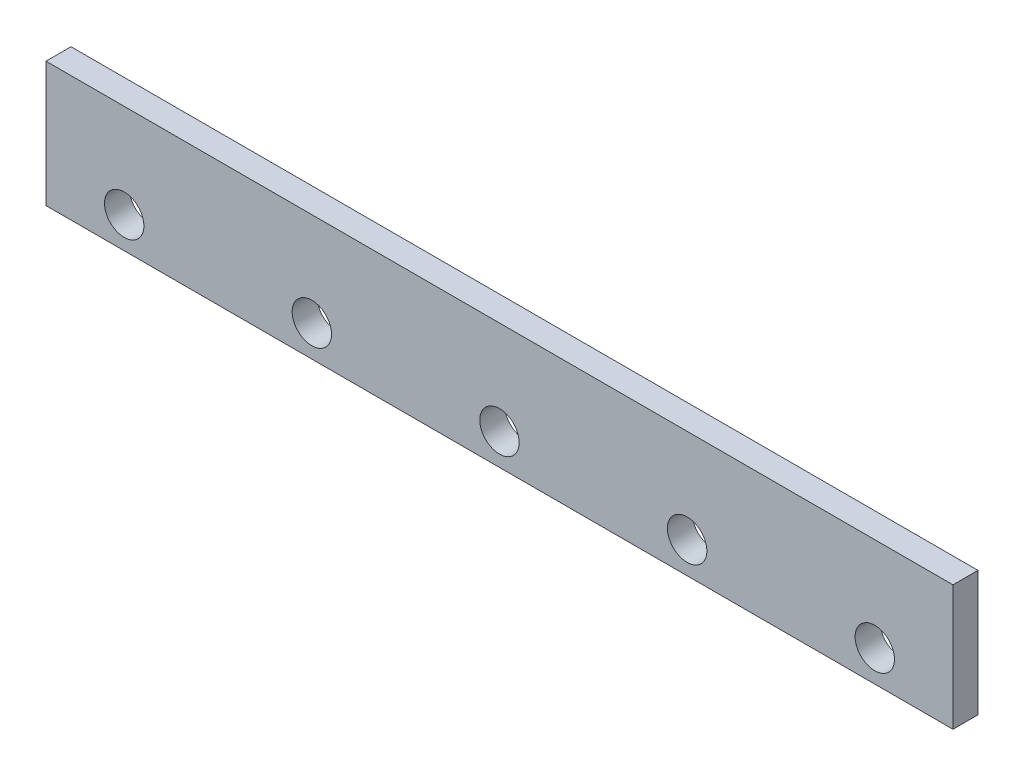
SolidWorks part; units mm, degrees
ref_plane "Front" through (0, 0, 0) normal (0, 0, 1) x (1, 0, 0)
ref_plane "Top" through (0, 0, 0) normal (0, 1, 0) x (1, 0, 0)
ref_plane "Right" through (0, 0, 0) normal (1, 0, 0) x (0, 0, -1)
sketch "Sketch1" plane through (0, 0, 0) normal (0, 0, 1) x (1, 0, 0)
  line L1 (290, -40) -> (-290, -40)
  line L2 (290, -40) -> (290, 40)
  line L3 (290, 40) -> (-290, 40)
  line L4 (-290, -40) -> (-290, 40)
  line L5 (290, -40) -> (-290, 40) construction
  line L6 (290, 40) -> (-290, -40) construction
  point P1 (0, 0)
  dimension "D1" = 580
  dimension "D2" = 80
extrude "Boss-Extrude1" add sketch "Sketch1" along normal blind 16
sketch "Sketch2" plane through (0, 0, 16) normal (0, 0, 1) x (1, 0, 0)
  line L0 (-290, 40) -> (-290, -40) construction
  line L2 (-290, -40) -> (290, -40) construction
  line L3 (290, -40) -> (290, 40) construction
  circle A0 centre (-240, -20) radius 12.6
  circle A1 centre (-120, -20) radius 12.6
  circle A2 centre (0, -20) radius 12.6
  circle A3 centre (120, -20) radius 12.6
  circle A4 centre (240, -20) radius 12.6
  point P14 (-241.1768, -40)
  point P15 (-240, -20)
  point P16 (0, -20)
  point P17 (0, 0)
  point P18 (0, 0)
  point P19 (-120.2831, -20)
  point P22 (-120, -20)
  point P23 (120, -20)
  point P24 (240, -20)
  point P25 (120, -20)
  point P26 (0, -20)
  point P27 (-120, -20)
  point P28 (-240, -20)
  dimension "D1" = 5
  dimension "D4" = 50
  dimension "D2" = 50
  dimension "D3" = 20
extrude "Cut-Extrude1" cut sketch "Sketch2" against normal blind 16
